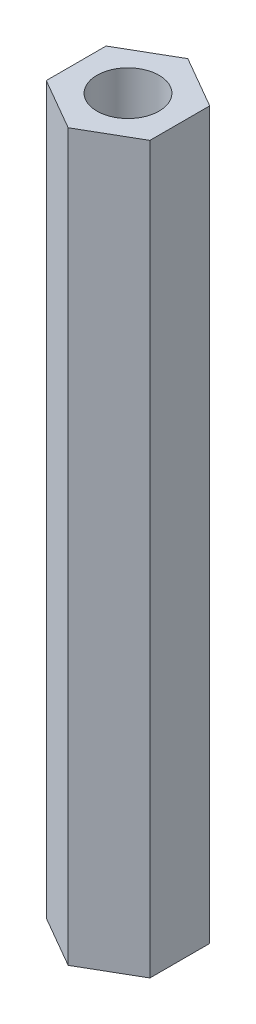
SolidWorks part; units mm, degrees
ref_plane "Front Plane" through (0, 0, 0) normal (0, 0, 1) x (1, 0, 0)
ref_plane "Top Plane" through (0, 0, 0) normal (0, 1, 0) x (1, 0, 0)
ref_plane "Right Plane" through (0, 0, 0) normal (1, 0, 0) x (0, 0, -1)
sketch "Sketch1" plane through (0, 0, 0) normal (0, 1, 0) x (1, 0, 0)
  line L1 (0, -3.6662) -> (3.175, -1.8331)
  line L2 (3.175, -1.8331) -> (3.175, 1.8331)
  line L3 (3.175, 1.8331) -> (0, 3.6662)
  line L4 (0, 3.6662) -> (-3.175, 1.8331)
  line L5 (-3.175, 1.8331) -> (-3.175, -1.8331)
  line L6 (-3.175, -1.8331) -> (0, -3.6662)
  circle A0 centre (0, 0) radius 3.175 construction
  circle A1 centre (0, 0) radius 1.905
  dimension "D2" = 3.81
  dimension "D1" = 6.35
extrude "Boss-Extrude1" add sketch "Sketch1" along normal blind 44.45
